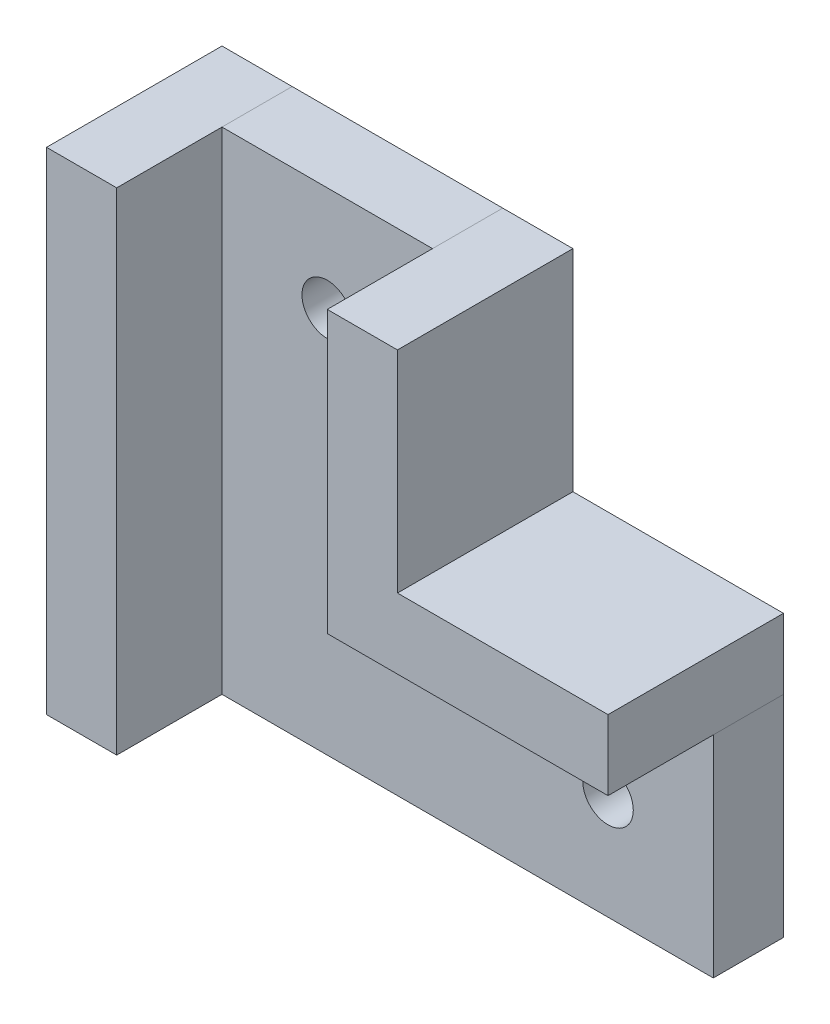
SolidWorks part; units mm, degrees
ref_plane "前视基准面" through (0, 0, 0) normal (0, 0, 1) x (1, 0, 0)
ref_plane "上视基准面" through (0, 0, 0) normal (0, 1, 0) x (1, 0, 0)
ref_plane "右视基准面" through (0, 0, 0) normal (1, 0, 0) x (0, 0, -1)
sketch "Sketch1" plane through (0, 0, 0) normal (0, 0, 1) x (1, 0, 0)
  line L0 (-7.5299, -25.8068) -> (27.4701, -25.8068)
  line L3 (-7.5299, 9.1932) -> (7.4701, 9.1932)
  line L4 (-7.5299, 9.1932) -> (-7.5299, -25.8068)
  line L6 (7.4701, 9.1932) -> (7.4701, -10.8068)
  line L7 (27.4701, -25.8068) -> (27.4701, -10.8068)
  line L8 (27.4701, -10.8068) -> (7.4701, -10.8068)
  dimension "D1" = 15
  dimension "D2" = 35
  dimension "D3" = 35
  dimension "D4" = 15
extrude "Boss-Extrude1" add sketch "Sketch1" along normal blind 5
sketch "Sketch2" plane through (0, 0, 0) normal (0, 0, -1) x (-1, 0, 0)
  line L0 (-7.4701, 9.1932) -> (-12.4701, 9.1932)
  line L1 (-12.4701, 9.1932) -> (-12.4701, -5.8068)
  line L2 (-12.4701, -5.8068) -> (-27.4701, -5.8068)
  line L3 (-27.4701, -10.8068) -> (-27.4701, -5.8068)
  line L4 (-27.4701, -10.8068) -> (-7.4701, -10.8068)
  line L5 (-7.4701, -10.8068) -> (-7.4701, 9.1932)
  dimension "D1" = 5
  dimension "D2" = 5
extrude "Boss-Extrude2" add sketch "Sketch2" against normal blind 12.5 separate body
sketch "Sketch3" plane through (0, 0, 0) normal (0, 0, -1) x (-1, 0, 0)
  line L0 (7.5299, 9.1932) -> (12.5299, 9.1932)
  line L1 (7.5299, -25.8068) -> (12.5299, -25.8068)
  line L2 (12.5299, -25.8068) -> (12.5299, 9.1932)
  line L3 (7.5299, -25.8068) -> (7.5299, 9.1932)
  dimension "D1" = 5
extrude "Boss-Extrude3" add sketch "Sketch3" against normal blind 12.5 separate body
sketch "Sketch4" plane through (0, 0, 0) normal (0, 0, -1) x (-1, 0, 0)
  line L0 (-27.4701, -10.8068) -> (-7.4701, -10.8068) construction
  line L1 (-27.4701, -25.8068) -> (-27.4701, -10.8068) construction
  line L2 (-7.4701, -10.8068) -> (-7.4701, 9.1932) construction
  line L3 (-7.4701, 9.1932) -> (7.5299, 9.1932) construction
  circle A0 centre (0.0299, 1.6932) radius 1.8
  circle A1 centre (-19.9701, -18.3068) radius 1.8
  dimension "D1" = 3.6
  dimension "D2" = 3.6
  dimension "D3" = 7.5
  dimension "D4" = 7.5
  dimension "D5" = 7.5
  dimension "D6" = 7.5
extrude "Cut-Extrude1" cut sketch "Sketch4" against normal through all
